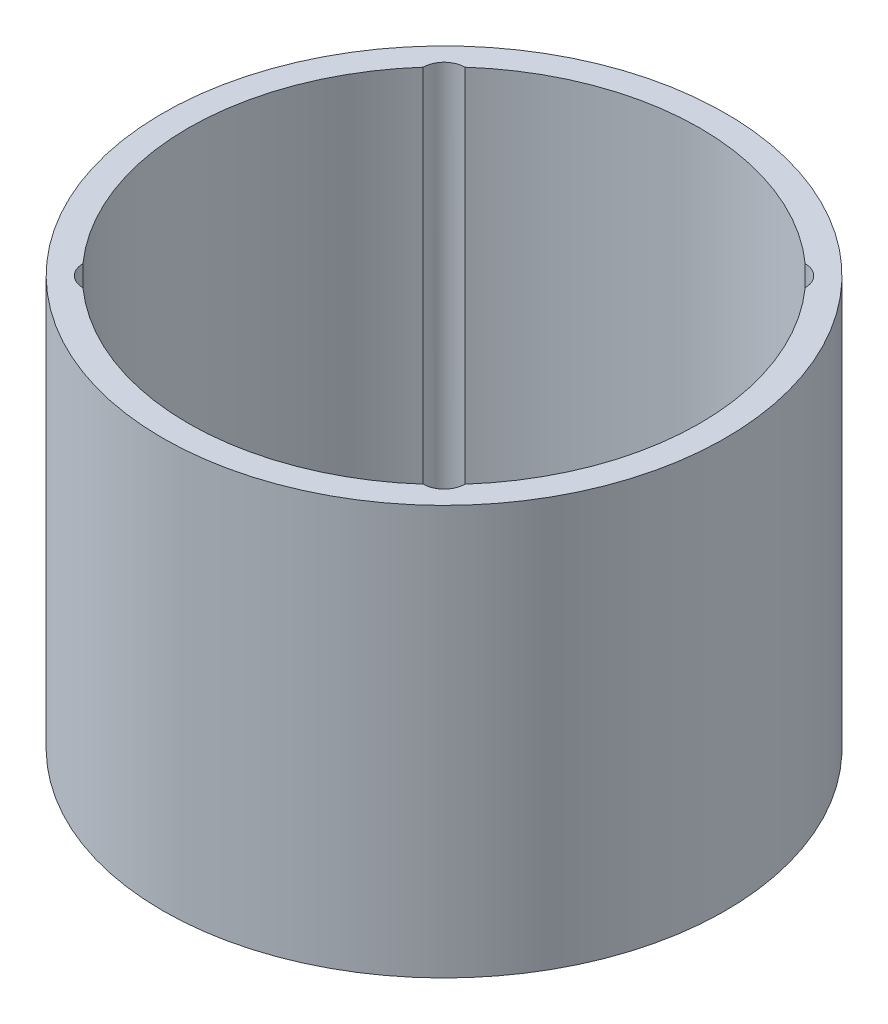
SolidWorks part; units mm, degrees
ref_plane "Спереди" through (0, 0, 0) normal (0, 0, 1) x (1, 0, 0)
ref_plane "Сверху" through (0, 0, 0) normal (0, 1, 0) x (1, 0, 0)
ref_plane "Справа" through (0, 0, 0) normal (1, 0, 0) x (0, 0, -1)
sketch "Sketch1" plane through (0, 0, 0) normal (0, 1, 0) x (1, 0, 0)
  circle A0 centre (0, 0) radius 55
  dimension "D1" = 110
extrude "Boss-Extrude1" add sketch "Sketch1" along normal blind 80
shell "Shell1" thickness 5
sketch "Sketch2" plane through (0, 80, 0) normal (0, 1, 0) x (1, 0, 0)
  line L1 (33.234, 33.234) -> (-33.234, 33.234) construction
  line L2 (33.234, 33.234) -> (33.234, -33.234) construction
  line L3 (33.234, -33.234) -> (-33.234, -33.234) construction
  line L4 (-33.234, 33.234) -> (-33.234, -33.234) construction
  line L5 (33.234, 33.234) -> (-33.234, -33.234) construction
  line L6 (33.234, -33.234) -> (-33.234, 33.234) construction
  circle A0 centre (0, 0) radius 47 construction
  circle A1 centre (0, 0) radius 55 construction
  circle A2 centre (-33.234, -33.234) radius 4.1
  circle A3 centre (-33.234, 33.234) radius 4.1
  circle A4 centre (33.234, 33.234) radius 4.1
  circle A5 centre (33.234, -33.234) radius 4.1
  dimension "D1" = 8
  dimension "D2" = 8.2
extrude "Cut-Extrude1" cut sketch "Sketch2" against normal through all
